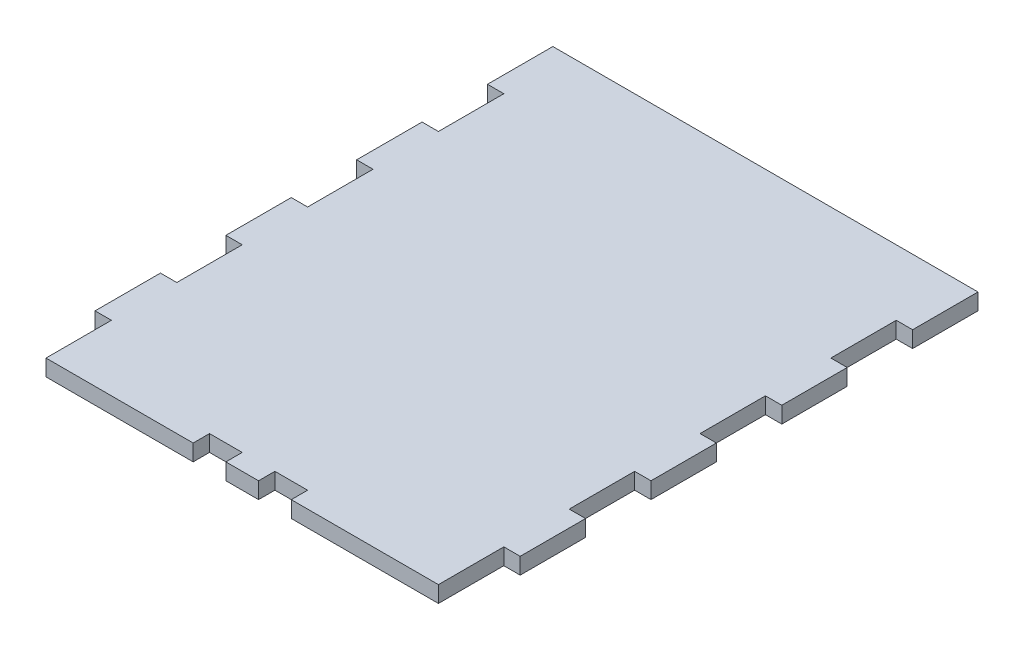
SolidWorks part; units mm, degrees
ref_plane "Front Plane" through (0, 0, 0) normal (0, 0, 1) x (1, 0, 0)
ref_plane "Top Plane" through (0, 0, 0) normal (0, 1, 0) x (1, 0, 0)
ref_plane "Right Plane" through (0, 0, 0) normal (1, 0, 0) x (0, 0, -1)
sketch "Sketch1" plane through (0, 0, 0) normal (0, 1, 0) x (1, 0, 0)
  line L0 (0, 0) -> (76.2, 0)
  line L1 (76.2, 12.7) -> (79.375, 12.7)
  line L2 (79.375, 12.7) -> (79.375, 25.4)
  line L3 (79.375, 25.4) -> (76.2, 25.4)
  line L4 (76.2, 25.4) -> (76.2, 38.1)
  line L5 (76.2, 38.1) -> (79.375, 38.1)
  line L6 (79.375, 38.1) -> (79.375, 50.8)
  line L7 (79.375, 50.8) -> (76.2, 50.8)
  line L8 (76.2, 50.8) -> (76.2, 63.5)
  line L9 (76.2, 63.5) -> (79.375, 63.5)
  line L10 (79.375, 63.5) -> (79.375, 76.2)
  line L11 (79.375, 76.2) -> (76.2, 76.2)
  line L12 (76.2, 76.2) -> (76.2, 88.9)
  line L13 (76.2, 88.9) -> (79.375, 88.9)
  line L14 (79.375, 88.9) -> (79.375, 101.6)
  line L15 (79.375, 101.6) -> (-3.175, 101.6)
  line L16 (-3.175, 101.6) -> (-3.175, 88.9)
  line L17 (-3.175, 88.9) -> (0, 88.9)
  line L18 (0, 88.9) -> (0, 76.2)
  line L19 (0, 76.2) -> (-3.175, 76.2)
  line L20 (-3.175, 76.2) -> (-3.175, 63.5)
  line L21 (-3.175, 63.5) -> (0, 63.5)
  line L22 (0, 63.5) -> (0, 50.8)
  line L23 (0, 50.8) -> (-3.175, 50.8)
  line L24 (-3.175, 50.8) -> (-3.175, 38.1)
  line L25 (-3.175, 38.1) -> (0, 38.1)
  line L26 (0, 38.1) -> (0, 25.4)
  line L27 (0, 25.4) -> (-3.175, 25.4)
  line L28 (-3.175, 25.4) -> (-3.175, 12.7)
  line L29 (-3.175, 12.7) -> (0, 12.7)
  line L30 (0, 12.7) -> (0, 0)
  line L31 (76.2, 12.7) -> (76.2, 0)
  line L32 (38.1, 0) -> (38.1, 101.6) construction
  dimension "D1" = 38.1
  dimension "D2" = 12.7
  dimension "D3" = 3.175
extrude "Boss-Extrude1" add sketch "Sketch1" along normal blind 3.175
sketch "Sketch2" plane through (0, 3.175, 0) normal (0, 1, 0) x (1, 0, 0)
  line L0 (38.1, 0) -> (38.1, 101.6) construction
  line L1 (0, 0) -> (76.2, 0) construction
  line L2 (79.375, 101.6) -> (-3.175, 101.6) construction
  line L3 (41.275, 0) -> (47.625, 0)
  line L4 (34.925, 0) -> (28.575, 0)
  line L5 (34.925, 0) -> (34.925, 3.175)
  line L6 (34.925, 3.175) -> (28.575, 3.175)
  line L7 (28.575, 0) -> (28.575, 3.175)
  line L8 (41.275, 0) -> (41.275, 3.175)
  line L9 (41.275, 3.175) -> (47.625, 3.175)
  line L10 (47.625, 0) -> (47.625, 3.175)
  dimension "D1" = 6.35
  dimension "D2" = 3.175
  dimension "D3" = 3.175
extrude "Cut-Extrude1" cut sketch "Sketch2" against normal through all
